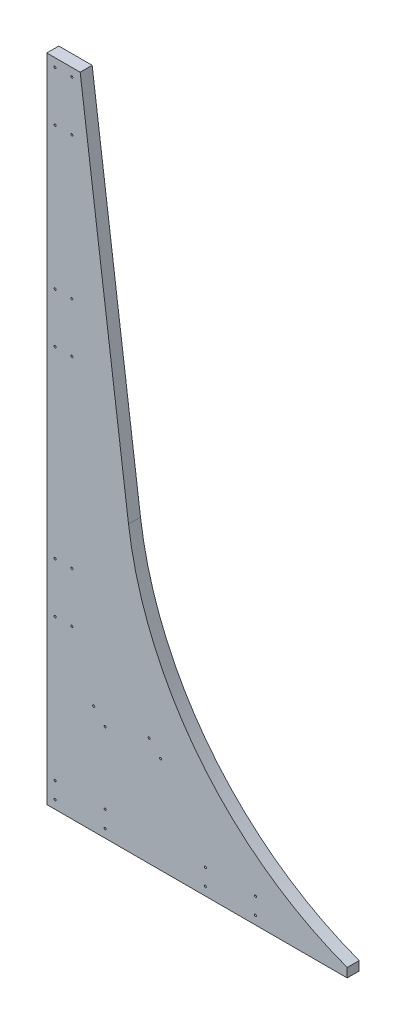
SolidWorks part; units mm, degrees
material "Pine"
ref_plane "Front Plane" through (0, 0, 0) normal (0, 0, 1) x (1, 0, 0)
ref_plane "Top Plane" through (0, 0, 0) normal (0, 1, 0) x (1, 0, 0)
ref_plane "Right Plane" through (0, 0, 0) normal (1, 0, 0) x (0, 0, -1)
sketch "Sketch1" plane through (0, 0, 0) normal (0, 0, 1) x (1, 0, 0)
  line L0 (0, 0) -> (500, 0)
  line L1 (0, 0) -> (0, 990.6)
  line L3 (0, 990.6) -> (50.8, 990.6)
  line L4 (50.8, 990.6) -> (124.3674, 431.8)
  line L7 (457.201, 13.862) -> (457.201, 0)
  arc A9 (124.3674, 431.8) -> (500, 0) centre (638.1166, 499.4364) ccw
  dimension "D18" = 50.8
  dimension "D1" = 500
  dimension "D2" = 990.6
  dimension "D3" = 42.799
  dimension "D4" = 50.8
  dimension "D5" = 558.8
  dimension "D6" = 97.5
extrude "Boss-Extrude1" add sketch "Sketch1" along normal blind 18.2562
sketch "Sketch2" plane through (0, 0, 18.2562) normal (0, 0, 1) x (1, 0, 0)
  line L0 (0, 990.6) -> (50.8, 990.6) construction
  line L1 (0, 0) -> (0, 990.6) construction
  line L2 (12.7, 977.9) -> (38.1, 977.9) construction
  line L3 (38.1, 977.9) -> (38.1, 901.7) construction
  line L4 (38.1, 901.7) -> (12.7, 901.7) construction
  line L5 (12.7, 901.7) -> (12.7, 977.9) construction
  line L6 (12.7, 901.7) -> (12.7, 685.8) construction
  line L7 (12.7, 609.6) -> (38.1, 609.6) construction
  line L8 (12.7, 685.8) -> (12.7, 609.6) construction
  line L9 (38.1, 685.8) -> (12.7, 685.8) construction
  line L10 (12.7, 254) -> (12.7, 38.1) construction
  line L11 (12.7, 254) -> (12.7, 330.2) construction
  line L12 (12.7, 330.2) -> (38.1, 330.2) construction
  line L13 (38.1, 330.2) -> (38.1, 254) construction
  line L14 (38.1, 254) -> (12.7, 254) construction
  line L15 (12.7, 38.1) -> (88.9, 38.1) construction
  line L16 (88.9, 38.1) -> (88.9, 12.7) construction
  line L17 (88.9, 12.7) -> (12.7, 12.7) construction
  line L18 (12.7, 12.7) -> (12.7, 38.1) construction
  line L20 (88.9, 38.1) -> (241.3, 38.1) construction
  line L21 (241.3, 38.1) -> (317.5, 38.1) construction
  line L22 (317.5, 38.1) -> (317.5, 12.7) construction
  line L23 (317.5, 12.7) -> (241.3, 12.7) construction
  line L24 (241.3, 12.7) -> (241.3, 38.1) construction
  circle A0 centre (12.7, 977.9) radius 1.5875
  circle A1 centre (38.1, 977.9) radius 1.5875
  circle A2 centre (12.7, 901.7) radius 1.5875
  circle A3 centre (38.1, 901.7) radius 1.5875
  circle A4 centre (12.7, 609.6) radius 1.5875
  circle A5 centre (38.1, 609.6) radius 1.5875
  circle A6 centre (12.7, 685.8) radius 1.5875
  circle A7 centre (38.1, 685.8) radius 1.5875
  circle A8 centre (12.7, 254) radius 1.5875
  circle A9 centre (38.1, 254) radius 1.5875
  circle A10 centre (12.7, 330.2) radius 1.5875
  circle A11 centre (38.1, 330.2) radius 1.5875
  circle A12 centre (12.7, 38.1) radius 1.5875
  circle A13 centre (12.7, 12.7) radius 1.5875
  circle A14 centre (88.9, 38.1) radius 1.5875
  circle A15 centre (88.9, 12.7) radius 1.5875
  circle A16 centre (241.3, 38.1) radius 1.5875
  circle A17 centre (317.5, 38.1) radius 1.5875
  circle A18 centre (241.3, 12.7) radius 1.5875
  circle A19 centre (317.5, 12.7) radius 1.5875
  dimension "D1" = 3.175
  dimension "D3" = 25.4
  dimension "D4" = 12.7
  dimension "D10" = 279.4
  dimension "D13" = 215.9
  dimension "D2" = 12.7
  dimension "D5" = 76.2
  dimension "D6" = 215.9
  dimension "D7" = 76.2
  dimension "D8" = 25.4
  dimension "D9" = 25.4
  dimension "D11" = 76.2
  dimension "D12" = 25.4
  dimension "D14" = 25.4
  dimension "D15" = 76.2
  dimension "D16" = 25.4
  dimension "D17" = 76.2
  dimension "D18" = 152.4
extrude "Cut-Extrude1" cut sketch "Sketch2" against normal through all
sketch "Sketch3" plane through (0, 0, 18.2562) normal (0, 0, 1) x (1, 0, 0)
  line L0 (88.9, 147.1124) -> (173.2788, 147.1124) construction
  line L1 (71.4248, 165.5274) -> (155.8036, 165.5274) construction
  line L4 (0, 0) -> (0, 990.6) construction
  circle A0 centre (88.9, 147.1124) radius 1.5875
  circle A1 centre (71.4248, 165.5274) radius 1.5875
  circle A2 centre (155.8036, 165.5274) radius 1.5875
  circle A3 centre (173.2788, 147.1124) radius 1.5875
  dimension "D1" = 3.175
  dimension "D2" = 88.9
  dimension "D3" = 18.415
  dimension "D4" = 84.3788
  dimension "D5" = 84.3788
  dimension "D6" = 17.4752
extrude "Cut-Extrude2" cut sketch "Sketch3" against normal through all
